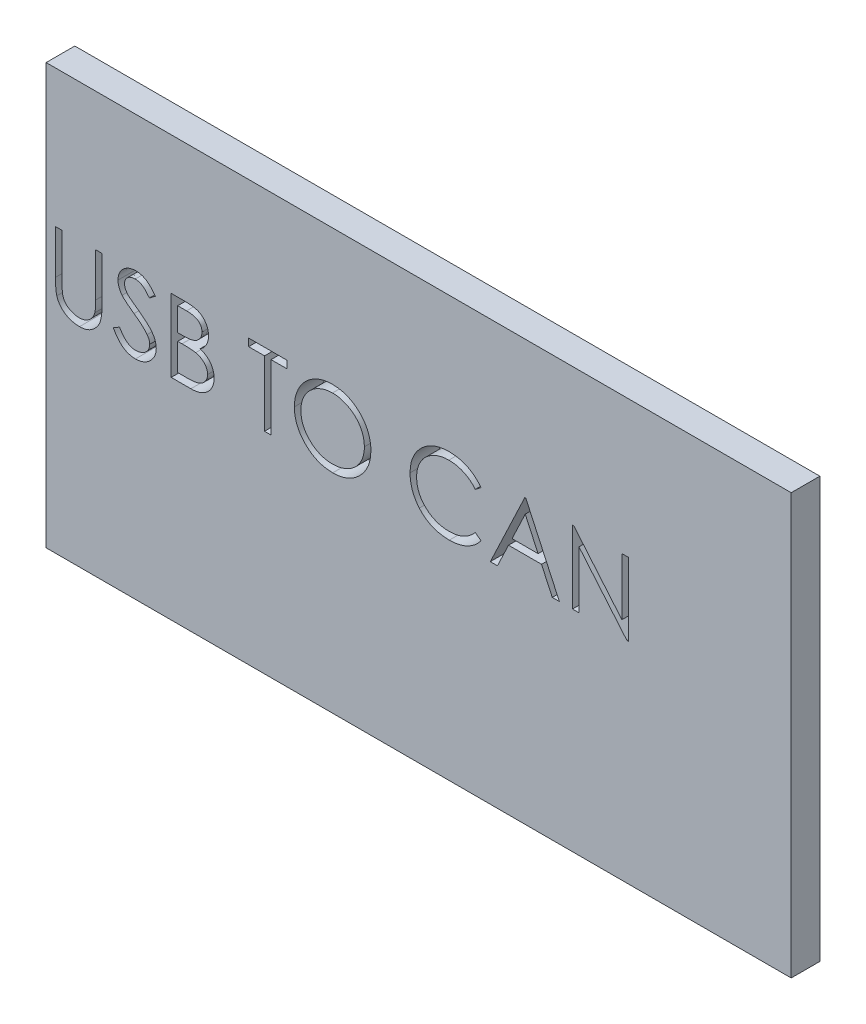
SolidWorks part; units mm, degrees
ref_plane "Front Plane" through (0, 0, 0) normal (0, 0, 1) x (1, 0, 0)
ref_plane "Top Plane" through (0, 0, 0) normal (0, 1, 0) x (1, 0, 0)
ref_plane "Right Plane" through (0, 0, 0) normal (1, 0, 0) x (0, 0, -1)
sketch "Sketch1" plane through (0, 0, 0) normal (0, 0, 1) x (1, 0, 0)
  line L1 (-39, 22) -> (39, 22)
  line L2 (-39, 22) -> (-39, -22)
  line L3 (-39, -22) -> (39, -22)
  line L4 (39, 22) -> (39, -22)
  line L5 (-39, 22) -> (39, -22) construction
  line L6 (-39, -22) -> (39, 22) construction
  point P0 (0, 0)
  dimension "D1" = 78
  dimension "D2" = 44
extrude "Boss-Extrude1" add sketch "Sketch1" along normal blind 3
sketch "Sketch2" plane through (0, 0, 3) normal (0, 0, 1) x (1, 0, 0)
  line L0 (-39, 0) -> (39, 0) construction
  line L1 (-39, 22) -> (-39, -22) construction
  line L2 (39, -22) -> (39, 22) construction
  text T0 "USB TO CAN" font "Century Gothic" height 7.62
extrude "Cut-Extrude1" cut sketch "Sketch2" against normal through all both and the other way through all
